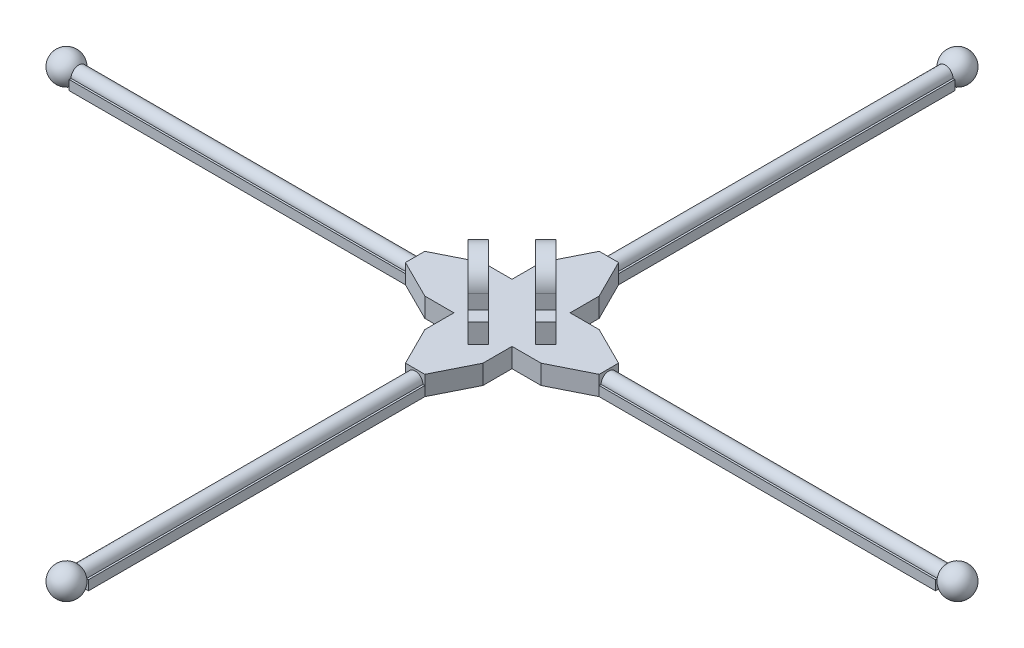
SolidWorks part; units mm, degrees
material "35钢"
ref_plane "前视基准面" through (0, 0, 0) normal (0, 0, 1) x (1, 0, 0)
ref_plane "上视基准面" through (0, 0, 0) normal (0, 1, 0) x (1, 0, 0)
ref_plane "右视基准面" through (0, 0, 0) normal (1, 0, 0) x (0, 0, -1)
sketch "草图1" plane through (0, 0, 0) normal (0, 1, 0) x (1, 0, 0)
  line L0 (3, -3) -> (6, -3)
  line L1 (-1, -10) -> (1, -10)
  line L3 (3, -3) -> (3, -6)
  line L4 (3, -6) -> (1, -10)
  line L11 (-3, -3) -> (-3, -6)
  line L12 (-3, -6) -> (-1, -10)
  line L13 (-10, 1) -> (-10, -1)
  line L14 (-3, -3) -> (-6, -3)
  line L15 (-6, -3) -> (-10, -1)
  line L16 (-3, 3) -> (-6, 3)
  line L17 (-6, 3) -> (-10, 1)
  line L18 (1, 10) -> (-1, 10)
  line L19 (-3, 3) -> (-3, 6)
  line L20 (-3, 6) -> (-1, 10)
  line L21 (3, 3) -> (3, 6)
  line L22 (3, 6) -> (1, 10)
  line L23 (10, -1) -> (10, 1)
  line L24 (3, 3) -> (6, 3)
  line L25 (6, 3) -> (10, 1)
  line L27 (6, -3) -> (10, -1)
  line L28 (3, -3) -> (6, -3) [skipped]
  point P34 (0, 0)
  dimension "D1" = 4
extrude "凸台-拉伸1" add sketch "草图1" along normal blind 2
sketch "草图2" plane through (0, 0, 10) normal (0, 0, 1) x (1, 0, 0)
  line L0 (0, 2) -> (0, 0) construction
  line L1 (-1, 2) -> (1, 2) construction
  circle A0 centre (0, 1) radius 0.8
extrude "切除-拉伸1" cut sketch "草图2" against normal blind 4
sketch "草图3" plane through (10, 0, 0) normal (1, 0, 0) x (0, 0, -1)
  line L0 (0, 2) -> (0, 0) construction
  line L1 (-1, 2) -> (1, 2) construction
  circle A0 centre (0, 1) radius 0.8
extrude "切除-拉伸2" cut sketch "草图3" against normal blind 4
sketch "草图4" plane through (0, 0, -10) normal (0, 0, -1) x (-1, 0, 0)
  line L0 (0, 2) -> (0, 0) construction
  line L1 (-1, 2) -> (1, 2) construction
  circle A0 centre (0, 1) radius 0.8
extrude "切除-拉伸3" cut sketch "草图4" against normal blind 4
sketch "草图5" plane through (-10, 0, 0) normal (-1, 0, 0) x (0, 0, 1)
  line L0 (0, 2) -> (0, 0) construction
  line L1 (-1, 2) -> (1, 2) construction
  circle A0 centre (0, 1) radius 0.8
extrude "切除-拉伸4" cut sketch "草图5" against normal blind 4
sketch "草图6" plane through (0, 0, 0) normal (0, 1, 0) x (1, 0, 0)
  line L0 (-3, 3) -> (3, -3) construction
ref_plane "基准面1" through (0, 0, 0) normal (-0.7071, 0, 0.7071) x (0.7071, 0, 0.7071)
ref_plane "基准面2" through (-1.2021, 0, 1.2021) normal (-0.7071, 0, 0.7071) x (0.7071, 0, 0.7071)
sketch "草图9" plane through (-1.2021, 0, 1.2021) normal (-0.7071, 0, 0.7071) x (0.7071, 0, 0.7071)
  line L0 (0, 2) -> (0, 5.5) construction
  line L1 (2.5, 5.5) -> (2.5, 4)
  line L2 (2.5, 4) -> (4, 4)
  line L3 (4, 4) -> (4, 2)
  line L4 (2.1213, 2) -> (6.364, 2) construction
  line L5 (4, 2) -> (-4, 2)
  line L6 (-6.364, 2) -> (-2.1213, 2) construction
  line L7 (-4, 2) -> (-4, 4)
  line L8 (-4, 4) -> (-2.5, 4)
  line L9 (-2.5, 4) -> (-2.5, 5.5)
  arc A0 (2.5, 5.5) -> (-2.5, 5.5) centre (0, 5.5) ccw
  circle A1 centre (0, 5.5) radius 1.5
  dimension "D1" = 3.5
  dimension "D2" = 2
  dimension "D3" = 2
extrude "凸台-拉伸2" add sketch "草图9" along normal blind 1.5
mirror "镜向1" about plane through (0, 0, 0) normal (-0.7071, 0, 0.7071) of "凸台-拉伸2"
sketch "草图10" plane through (-6, 0, 0) normal (-1, 0, 0) x (0, 0, 1)
  circle A0 centre (0, 1) radius 0.8
extrude "凸台-拉伸3" add sketch "草图10" along normal blind 40
sketch "草图11" plane through (0, 0, 6) normal (0, 0, 1) x (1, 0, 0)
  circle A0 centre (0, 1) radius 0.8
extrude "凸台-拉伸4" add sketch "草图11" along normal blind 40
mirror "镜向2" about plane through (0, 0, 0) normal (0, 0, 1) of "凸台-拉伸4"
mirror "镜向3" about plane through (0, 0, 0) normal (1, 0, 0) of "凸台-拉伸3"
sketch "草图12" plane through (0, 0, 0) normal (1, 0, 0) x (0, 0, -1)
  line L2 (-46, 1.8) -> (-46, 0.2) construction
  line L3 (-47.5, 1) -> (-44.5, 1)
  arc A1 (-44.5, 1) -> (-47.5, 1) centre (-46, 1) ccw
revolve "旋转1" add sketch "草图12" angle 360 about L3
sketch "草图14" plane through (0, 0, 0) normal (0, 0, 1) x (1, 0, 0)
  line L0 (-46, 1.8) -> (-46, 0.2) construction
  line L1 (-47.5, 1) -> (-44.5, 1)
  arc A0 (-44.5, 1) -> (-47.5, 1) centre (-46, 1) ccw
revolve "旋转2" add sketch "草图14" angle 360 about L1
mirror "镜向4" about plane through (0, 0, 0) normal (0, 0, 1) of "旋转1"
mirror "镜向5" about plane through (0, 0, 0) normal (1, 0, 0) of "旋转2"
sketch "草图15" plane through (0, 0, 0) normal (0, 1, 0) x (1, 0, 0)
  line L0 (-1, 10) -> (1, 10)
  line L1 (1, 10) -> (1, 44.7311)
  line L2 (1, 44.7311) -> (-1, 44.7311)
  line L3 (-1, 44.7311) -> (-1, 10)
  line L4 (10, 1) -> (10, -1)
  line L5 (10, -1) -> (44.7311, -1)
  line L6 (44.7311, -1) -> (44.7311, 1)
  line L7 (44.7311, 1) -> (10, 1)
  line L8 (1, -10) -> (-1, -10)
  line L9 (-1, -10) -> (-1, -44.7311)
  line L10 (-1, -44.7311) -> (1, -44.7311)
  line L11 (1, -44.7311) -> (1, -10)
  line L12 (-10, -1) -> (-10, 1)
  line L13 (-10, 1) -> (-44.7311, 1)
  line L14 (-44.7311, 1) -> (-44.7311, -1)
  line L15 (-44.7311, -1) -> (-10, -1)
  point P21 (0, 0)
  dimension "D1" = 4
extrude "凸台-拉伸6" add sketch "草图15" along normal blind 1
